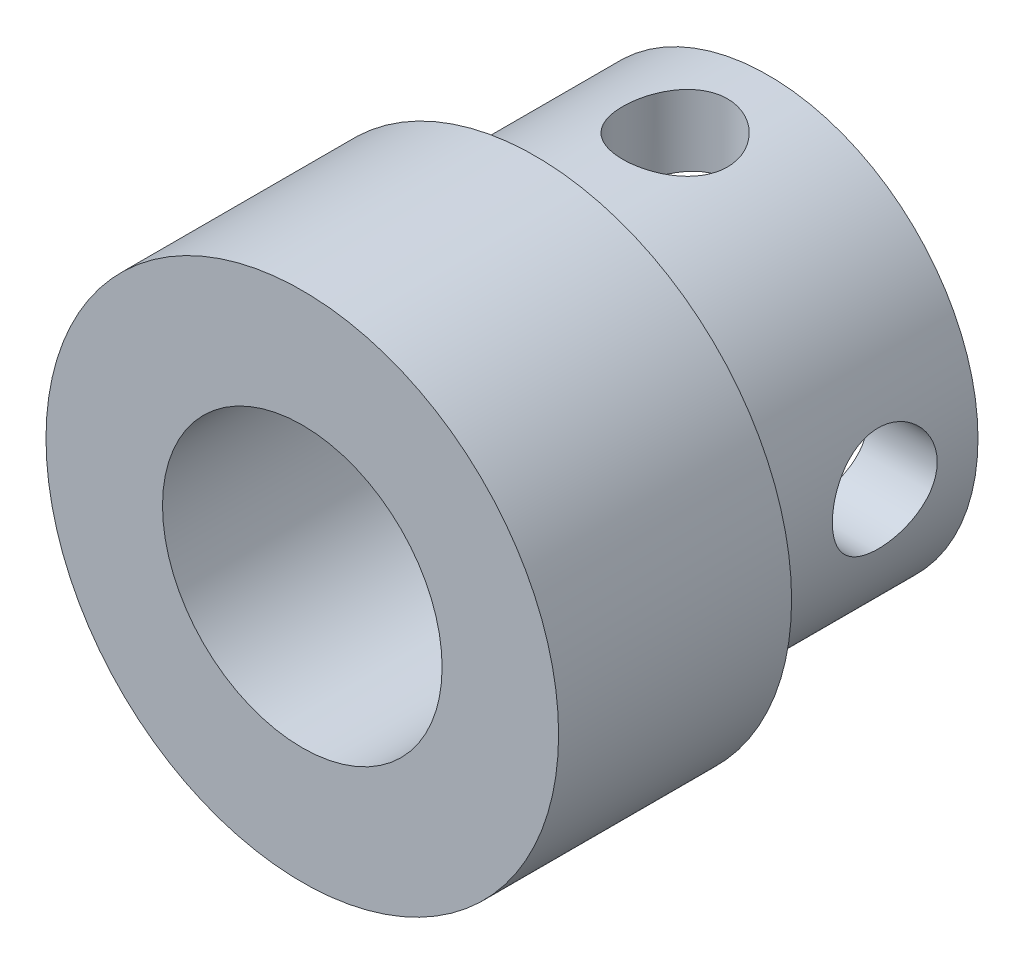
SolidWorks part; units mm, degrees
ref_plane "Plan de face" through (0, 0, 0) normal (0, 0, 1) x (1, 0, 0)
ref_plane "Plan de dessus" through (0, 0, 0) normal (0, 1, 0) x (1, 0, 0)
ref_plane "Plan de droite" through (0, 0, 0) normal (1, 0, 0) x (0, 0, -1)
sketch "Esquisse1" plane through (0, 0, 0) normal (0, 0, 1) x (1, 0, 0)
  circle A0 centre (0, 0) radius 11
  circle A1 centre (0, 0) radius 6
  dimension "D1" = 12
  dimension "D2" = 22
extrude "Boss.-Extru.1" add sketch "Esquisse1" along normal blind 10
sketch "Esquisse2" plane through (0, 0, 0) normal (0, 0, -1) x (-1, 0, 0)
  circle A0 centre (0, 0) radius 6
  circle A1 centre (0, 0) radius 9
  dimension "D1" = 12
  dimension "D2" = 18
extrude "Boss.-Extru.2" add sketch "Esquisse2" along normal blind 10
hole_wizard "Dégagement M41" positions "Esquisse3D1" profile "Esquisse3" hole size "M4" standard "ISO" end condition through all
sketch3d "Esquisse3D1"
  point P0 (0, 9, -6)
  point P2 (-9, 0, -6)
  dimension "D1" = 4
  dimension "D2" = 4
sketch "Esquisse3" plane through (0, 9, -6) normal (1, 0, 0) x (0, 0, 1)
  line L0 (0, 0) -> (0, 20)
  line L1 (0, 20) -> (2.25, 20)
  line L2 (2.25, 20) -> (2.25, 0)
  line L5 (2.25, 0) -> (0, 0)
  line L11 (0, -6.35) -> (0, 107.95) construction
  dimension "Diamètre du perçage jusqu'au prochain" = 4.5
  dimension "Profondeur du perçage jusqu'au prochain" = 20
